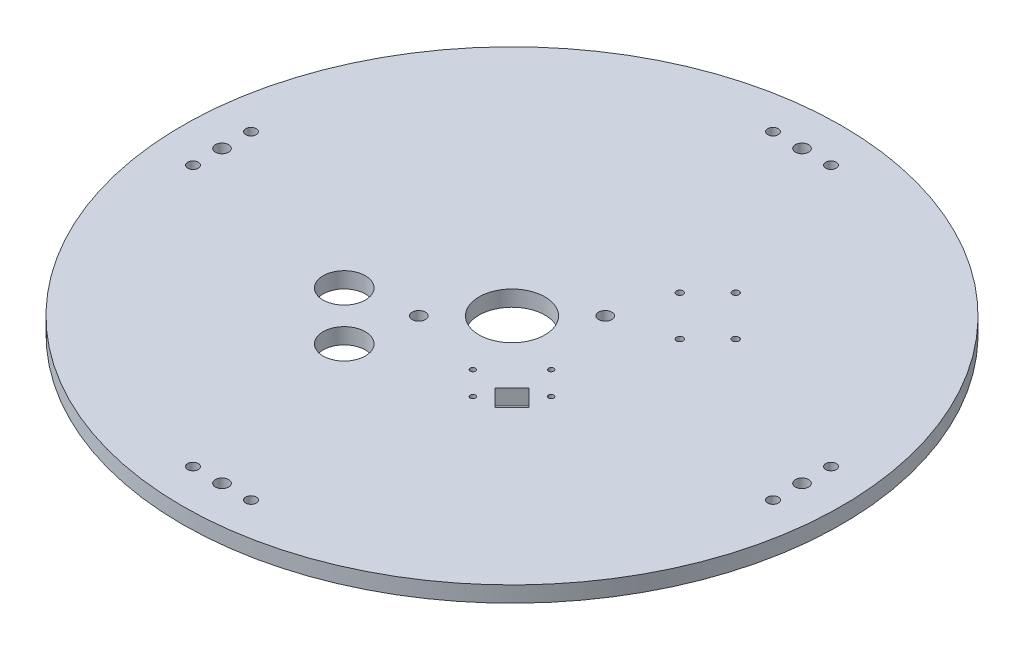
SolidWorks part; units mm, degrees
ref_plane "Front Plane" through (0, 0, 0) normal (0, 0, 1) x (1, 0, 0)
ref_plane "Top Plane" through (0, 0, 0) normal (0, 1, 0) x (1, 0, 0)
ref_plane "Right Plane" through (0, 0, 0) normal (1, 0, 0) x (0, 0, -1)
sketch "Sketch1" plane through (0, 0, 0) normal (0, 1, 0) x (1, 0, 0)
  circle A0 centre (0, 0) radius 125
  dimension "D1" = 250
extrude "Boss-Extrude1" add sketch "Sketch1" along normal blind 6
sketch "Sketch2" plane through (0, 0, 0) normal (0, 1, 0) x (1, 0, 0)
  circle A0 centre (0, 110) radius 2.5
  circle A1 centre (110, 0) radius 2.5
  circle A2 centre (0, -110) radius 2.5
  circle A3 centre (-110, 0) radius 2.5
  point P12 (0, 0)
  dimension "D1" = 5
  dimension "D2" = 110
  dimension "D3" = 4
extrude "Cut-Extrude1" cut sketch "Sketch2" along normal blind 6
sketch "Sketch3" plane through (0, 0, 0) normal (0, 1, 0) x (1, 0, 0)
  circle A0 centre (0, 0) radius 12.5
  dimension "D1" = 25
extrude "Cut-Extrude2" cut sketch "Sketch3" along normal blind 6
sketch "Sketch4" plane through (0, 0, 0) normal (0, 1, 0) x (1, 0, 0)
  line L1 (62.3315, 75.8372) -> (76.2615, 61.9072)
  line L2 (62.3315, 75.8372) -> (60.4223, 73.928)
  line L3 (60.4223, 73.928) -> (74.3523, 59.998)
  line L4 (76.2615, 61.9072) -> (74.3523, 59.998)
  line L5 (62.3315, 75.8372) -> (74.3523, 59.998) construction
  line L6 (60.4223, 73.928) -> (76.2615, 61.9072) construction
  line L7 (-62.3315, -75.8372) -> (-76.2615, -61.9072)
  line L8 (-62.3315, -75.8372) -> (-60.4223, -73.928)
  line L9 (-60.4223, -73.928) -> (-74.3523, -59.998)
  line L10 (-76.2615, -61.9072) -> (-74.3523, -59.998)
  line L11 (-62.3315, -75.8372) -> (-74.3523, -59.998) construction
  line L12 (-60.4223, -73.928) -> (-76.2615, -61.9072) construction
  circle A0 centre (72.5845, 72.1602) radius 2.5
  circle A1 centre (64.0992, 63.675) radius 2.5
  circle A2 centre (-72.5845, -72.1602) radius 2.5
  circle A3 centre (-64.0992, -63.675) radius 2.5
  point P0 (68.3419, 67.9176)
  point P7 (-68.3419, -67.9176)
  point P12 (0, 0)
  point P14 (0, 0)
  point P23 (0, 0)
  dimension "D6" = 5
  dimension "D7" = 5
  dimension "D8" = 12
  dimension "D9" = 6
  dimension "D1" = 19.7
  dimension "D2" = 2.7
  dimension "D3" = 95
  dimension "D4" = 10.15
  dimension "D5" = 2
  dimension "D10" = 2
sketch "Sketch5" plane through (0, 0, 0) normal (0, 1, 0) x (1, 0, 0)
  circle A0 centre (17.6777, 17.6777) radius 2.5
  circle A1 centre (-17.6777, -17.6777) radius 2.5
  dimension "D1" = 5
  dimension "D2" = 5
  dimension "D3" = 25
  dimension "D4" = 25
extrude "Cut-Extrude4" cut sketch "Sketch5" along normal blind 10
sketch "Sketch7" plane through (0, 0, 0) normal (0, 1, 0) x (1, 0, 0)
  line L0 (33.9411, -19.0919) -> (19.0919, -33.9411) construction
  line L1 (19.0919, -33.9411) -> (10.253, -25.1023) construction
  line L2 (10.253, -25.1023) -> (25.1023, -10.253) construction
  line L3 (25.1023, -10.253) -> (33.9411, -19.0919) construction
  line L5 (33.234, -26.8701) -> (26.8701, -33.234)
  line L6 (33.234, -26.8701) -> (26.8701, -20.5061)
  line L7 (26.8701, -20.5061) -> (20.5061, -26.8701)
  line L8 (26.8701, -33.234) -> (20.5061, -26.8701)
  line L9 (33.234, -26.8701) -> (20.5061, -26.8701) construction
  line L10 (26.8701, -20.5061) -> (26.8701, -33.234) construction
  circle A0 centre (33.9411, -19.0919) radius 1
  circle A1 centre (19.0919, -33.9411) radius 1
  circle A2 centre (25.1023, -10.253) radius 1
  circle A3 centre (10.253, -25.1023) radius 1
  point P8 (26.8701, -26.8701)
  dimension "D1" = 2
  dimension "D2" = 2
  dimension "D3" = 2
  dimension "D4" = 2
  dimension "D5" = 21
  dimension "D6" = 12.5
  dimension "D7" = 9
  dimension "D8" = 9
  dimension "D9" = 10.5
  dimension "D10" = 13
  dimension "D11" = 25
  dimension "D12" = 10.5
extrude "Cut-Extrude7" cut sketch "Sketch7" along normal blind 10
sketch "Sketch8" plane through (0, 0, 0) normal (0, 1, 0) x (1, 0, 0)
  line L0 (-11, -110) -> (11, -110) construction
  line L1 (-110, 11) -> (-110, -11) construction
  line L2 (11, 110) -> (-11, 110) construction
  line L3 (110, -11) -> (110, 11) construction
  circle A0 centre (-11, -110) radius 2
  circle A1 centre (11, -110) radius 2
  circle A2 centre (-110, 11) radius 2
  circle A3 centre (-110, -11) radius 2
  circle A4 centre (11, 110) radius 2
  circle A5 centre (-11, 110) radius 2
  circle A6 centre (110, -11) radius 2
  circle A7 centre (110, 11) radius 2
  point P21 (0, 0)
  dimension "D1" = 4
  dimension "D2" = 4
  dimension "D3" = 4
extrude "Cut-Extrude8" cut sketch "Sketch8" along normal blind 10
sketch "Sketch9" plane through (0, 0, 0) normal (0, 1, 0) x (1, 0, 0)
  line L0 (24.2184, 39.4212) -> (34.825, 50.0278) construction
  line L1 (34.825, 50.0278) -> (50.0278, 34.825) construction
  line L2 (50.0278, 34.825) -> (39.4212, 24.2184) construction
  line L3 (39.4212, 24.2184) -> (24.2184, 39.4212) construction
  circle A0 centre (34.825, 50.0278) radius 1.25
  circle A1 centre (24.2184, 39.4212) radius 1.25
  circle A2 centre (39.4212, 24.2184) radius 1.25
  circle A3 centre (50.0278, 34.825) radius 1.25
  point P12 (0, 0)
  point P13 (0, 0)
  point P14 (0, 0)
  point P15 (0, 0)
  dimension "D1" = 21.5
  dimension "D2" = 15
  dimension "D3" = 10.75
  dimension "D4" = 45
extrude "Cut-Extrude9" cut sketch "Sketch9" along normal blind 10
sketch "Sketch10" plane through (0, 0, 0) normal (0, 1, 0) x (1, 0, 0)
  line L0 (-22.6274, -41.0122) -> (-41.0122, -22.6274) construction
  line L1 (-31.8198, -31.8198) -> (0, 0) construction
  line L2 (0, 0) -> (0, 20.5469) construction
  circle A0 centre (-22.6274, -41.0122) radius 8
  circle A1 centre (-41.0122, -22.6274) radius 8
  dimension "D2" = 16
  dimension "D3" = 16
  dimension "D1" = 26
  dimension "D4" = 45
  dimension "D5" = 135
extrude "Cut-Extrude10" cut sketch "Sketch10" along normal blind 10
